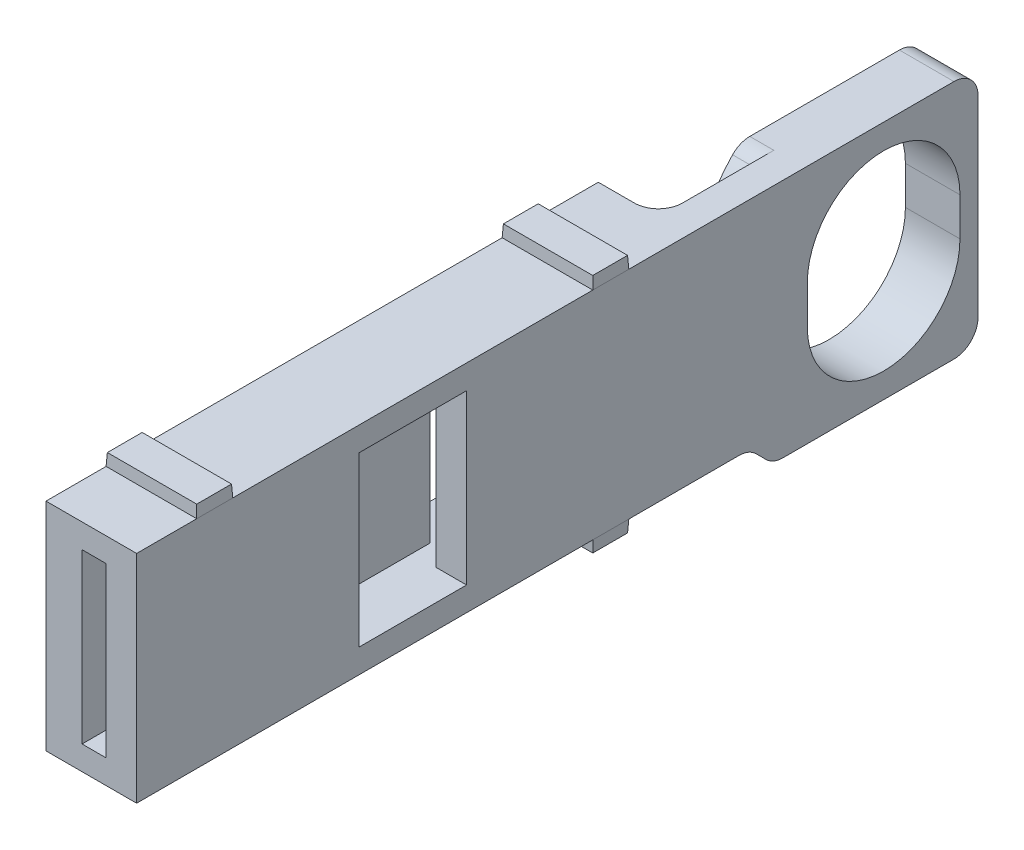
SolidWorks part; units mm, degrees
material "Nylon 6/10"
ref_plane "Front Plane" through (0, 0, 0) normal (0, 0, 1) x (1, 0, 0)
ref_plane "Top Plane" through (0, 0, 0) normal (0, 1, 0) x (1, 0, 0)
ref_plane "Right Plane" through (0, 0, 0) normal (1, 0, 0) x (0, 0, -1)
sketch "Sketch1" plane through (0, 0, 0) normal (1, 0, 0) x (0, 0, -1)
  line L0 (-6.35, 1.5875) -> (-6.35, -1.5875)
  line L1 (-62.15, 10) -> (7.85, 10)
  line L2 (-62.15, 10) -> (-62.15, -8)
  line L3 (-9.2, -10) -> (7.85, -10)
  line L4 (7.85, 10) -> (7.85, -10)
  line L5 (6.35, 1.5875) -> (6.35, -1.5875)
  line L6 (0, 1.5875) -> (0, -1.5875) construction
  line L7 (7.85, 0) -> (-62.15, 0) construction
  line L8 (-62.15, -8) -> (-11.2, -8)
  line L9 (-11.2, -8) -> (-9.2, -10)
  arc A0 (6.35, 1.5875) -> (-6.35, 1.5875) centre (0, 1.5875) ccw
  arc A1 (-6.35, -1.5875) -> (6.35, -1.5875) centre (0, -1.5875) ccw
  dimension "D1" = 12.7
  dimension "D2" = 3.175
  dimension "D3" = 1.5
  dimension "D4" = 20
  dimension "D5" = 45
  dimension "D6" = 18
  dimension "D7" = 70
  dimension "D8" = 19.05
extrude "Extrude1" add sketch "Sketch1" along normal blind 2.54
sketch "Sketch2" plane through (2.54, 0, 0) normal (1, 0, 0) x (0, 0, -1)
  spline S0 degree 3 poles (6.2978, 2.3998) (5.0148, 12.3471) (-5.0148, 12.3471) (-6.2978, 2.3998) (-6.3094, 2.3101) (-6.3287, 2.1302) (-6.35, 1.8588) (-6.35, 1.6779) (-6.35, 1.5875) (-6.35, 1.4993) (-6.35, 1.3229) (-6.35, 1.0583) (-6.35, 0.8819) (-6.35, 0.7938) (-6.35, 0.2646) (-6.35, -0.2646) (-6.35, -0.7937) (-6.35, -0.8819) (-6.35, -1.0583) (-6.35, -1.3229) (-6.35, -1.4993) (-6.35, -1.5875) (-6.35, -1.6779) (-6.35, -1.8588) (-6.3287, -2.1302) (-6.3094, -2.3101) (-6.2978, -2.3998) (-5.0148, -12.3471) (5.0148, -12.3471) (6.2978, -2.3998) (6.3094, -2.3101) (6.3287, -2.1302) (6.35, -1.8588) (6.35, -1.6779) (6.35, -1.5875) (6.35, -1.4993) (6.35, -1.3229) (6.35, -1.0583) (6.35, -0.8819) (6.35, -0.7938) (6.35, -0.2646) (6.35, 0.2646) (6.35, 0.7938) (6.35, 0.8819) (6.35, 1.0583) (6.35, 1.3229) (6.35, 1.4993) (6.35, 1.5875) (6.35, 1.6779) (6.35, 1.8588) (6.3287, 2.1302) (6.3094, 2.3101) (6.2978, 2.3998) (5.0148, 12.3471) (-5.0148, 12.3471) knots -0.007797 0 0 0 0.361974 0.361974 0.361974 0.369771 0.377568 0.385365 0.385365 0.385365 0.392969 0.400572 0.408176 0.408176 0.408176 0.453798 0.453798 0.453798 0.461401 0.469005 0.476608 0.476608 0.476608 0.484406 0.492203 0.5 0.5 0.5 0.861974 0.861974 0.861974 0.869771 0.877568 0.885365 0.885365 0.885365 0.892969 0.900572 0.908176 0.908176 0.908176 0.953798 0.953798 0.953798 0.961401 0.969005 0.976608 0.976608 0.976608 0.984406 0.992203 1 1 1 1.361974 1.361974 1.361974 weights 1 0.418613 0.418613 1 1 1 1 1 1 1 1 1 1 1 1 1 1 1 1 1 1 1 1 1 1 1 1 0.418613 0.418613 1 1 1 1 1 1 1 1 1 1 1 1 1 1 1 1 1 1 1 1 1 1 1 1 0.418613 0.418613 only from (6.2978, 2.3998) to (6.2978, 2.3998)
sketch "Sketch3" plane through (0, 0, 0) normal (-1, 0, 0) x (0, 0, 1)
  line L2 (6.35, 1.5875) -> (6.35, -1.5875) construction
  line L3 (-6.35, -1.5875) -> (-6.35, 1.5875) construction
  line L4 (11.2, -8) -> (11.2, 1.5875)
  line L8 (6.35, 1.5875) -> (6.35, -1.5875)
  line L9 (-6.35, -1.5875) -> (-6.35, 1.5875)
  line L12 (11.2, 1.5875) -> (11.2, -1.5875) construction
  line L15 (62.15, -8) -> (62.15, 10)
  line L16 (62.15, 10) -> (-7.85, 10)
  line L17 (-7.85, 10) -> (-7.85, -10)
  line L18 (-7.85, -10) -> (9.2, -10)
  line L19 (9.2, -10) -> (11.2, -8)
  line L20 (11.2, -8) -> (62.15, -8)
  line L22 (7.3939, 10) -> (-7.85, 10)
  line L23 (-7.85, 10) -> (-7.85, -10)
  line L24 (-7.85, -10) -> (9.2, -10)
  line L25 (9.2, -10) -> (11.2, -8)
  arc A2 (-6.35, -1.5875) -> (6.35, -1.5875) centre (0, -1.5875) ccw construction
  arc A3 (6.35, 1.5875) -> (-6.35, 1.5875) centre (0, 1.5875) ccw construction
  arc A4 (11.2, 1.5875) -> (7.3939, 10) centre (0, 1.5875) ccw
  arc A6 (11.2, 1.5875) -> (-11.2, 1.5875) centre (0, 1.5875) ccw construction
  arc A8 (-6.35, -1.5875) -> (6.35, -1.5875) centre (0, -1.5875) ccw
  arc A9 (6.35, 1.5875) -> (-6.35, 1.5875) centre (0, 1.5875) ccw
  dimension "D1" = 0
extrude "Extrude2" add sketch "Sketch3" along normal blind 2
sketch "Sketch4" plane through (0, 0, 0) normal (-1, 0, 0) x (0, 0, 1)
  line L0 (7.3939, 10) -> (62.15, 10) construction
  line L1 (16.2, 10) -> (62.15, 10)
  line L2 (16.2, 10) -> (16.2, -8)
  line L3 (16.2, -8) -> (62.15, -8)
  line L4 (62.15, 10) -> (62.15, -8)
  line L5 (18.2, 8) -> (60.15, 8)
  line L6 (11.2, -8) -> (11.2, 1.5875) construction
  line L7 (60.15, 8) -> (60.15, -6)
  line L8 (18.2, -6) -> (60.15, -6)
  line L9 (18.2, 8) -> (18.2, -6)
  dimension "D1" = 5
extrude "Extrude3" add sketch "Sketch4" along normal blind 5
sketch "Sketch5" plane through (0, 0, 0) normal (-1, 0, 0) x (0, 0, 1)
  line L0 (60.15, 8) -> (18.2, 8) construction
  line L1 (33.2, 8) -> (45.15, 8)
  line L2 (33.2, 8) -> (33.2, -6)
  line L3 (33.2, -6) -> (45.15, -6)
  line L4 (45.15, 8) -> (45.15, -6)
  line L5 (18.2, -6) -> (60.15, -6) construction
  line L6 (18.2, 8) -> (18.2, -6) construction
  line L7 (60.15, -6) -> (60.15, 8) construction
  point P8 (18.2, 1)
  dimension "D1" = 15
  dimension "D2" = 15
extrude "Extrude4" add sketch "Sketch5" along normal up to surface (5 mm away) up to face at (-5, 1, 39.175)
sketch "Sketch6" plane through (0, 0, 62.15) normal (0, 0, 1) x (1, 0, 0)
  line L0 (-5, 8) -> (0, 8) construction
  line L1 (-2, 8) -> (0, 8)
  line L2 (-2, 8) -> (-2, -6)
  line L3 (-2, -6) -> (0, -6)
  line L4 (0, 8) -> (0, -6)
  dimension "D1" = 2
extrude "Cut-Extrude1" cut sketch "Sketch6" against normal up to surface (43.95 mm away) up to face at (-2.5, 1, 18.2)
sketch "Sketch7" plane through (2.54, 0, 0) normal (1, 0, 0) x (0, 0, -1)
  line L0 (-62.15, 8) -> (-18.2, 8) construction
  line L1 (-43.65, 8) -> (-34.7, 8)
  line L2 (-43.65, 8) -> (-43.65, -6)
  line L3 (-43.65, -6) -> (-34.7, -6)
  line L4 (-34.7, 8) -> (-34.7, -6)
  line L5 (-18.2, -6) -> (-62.15, -6) construction
  line L6 (-33.2, 8) -> (-33.2, -6) construction
  line L7 (-45.15, -6) -> (-45.15, 8) construction
  dimension "D1" = 1.5
  dimension "D2" = 1.5
extrude "Cut-Extrude2" cut sketch "Sketch7" against normal up to next
fillet "Fillet1" radius 2 6 edges at (0.27, 10, -7.85) (0.27, -10, -7.85) (1.27, -8, 11.2) (0.27, -10, 9.2) (0, 1, 16.2)
sketch "Sketch8" plane through (0, 10, 0) normal (0, 1, 0) x (1, 0, 0)
  line L0 (-5, -62.15) -> (-5, -16.2) construction
  line L1 (-5, -21.2) -> (2.54, -21.2)
  line L2 (-5, -21.2) -> (-5, -24.2)
  line L3 (-5, -24.2) -> (2.54, -24.2)
  line L4 (2.54, -21.2) -> (2.54, -24.2)
  line L5 (2.54, 5.85) -> (2.54, -62.15) construction
  line L7 (-5, -54.15) -> (2.54, -54.15)
  line L8 (-5, -54.15) -> (-5, -57.15)
  line L9 (-5, -57.15) -> (2.54, -57.15)
  line L10 (2.54, -54.15) -> (2.54, -57.15)
  line L11 (-5, -16.2) -> (-2, -16.2) construction
  dimension "D1" = 3
  dimension "D2" = 3
  dimension "D3" = 5
  dimension "D4" = 5
extrude "Extrude5" add sketch "Sketch8" along normal blind 1 draft 3
sketch "Sketch9" plane through (0, -8, 0) normal (0, -1, 0) x (1, 0, 0)
  line L0 (-5, 16.2) -> (-5, 62.15) construction
  line L1 (-5, 24.2) -> (2.54, 24.2)
  line L2 (-5, 24.2) -> (-5, 21.2)
  line L3 (-5, 21.2) -> (2.54, 21.2)
  line L4 (2.54, 24.2) -> (2.54, 21.2)
  dimension "D1" = 3
extrude "Extrude6" add sketch "Sketch9" along normal blind 1 draft 3
